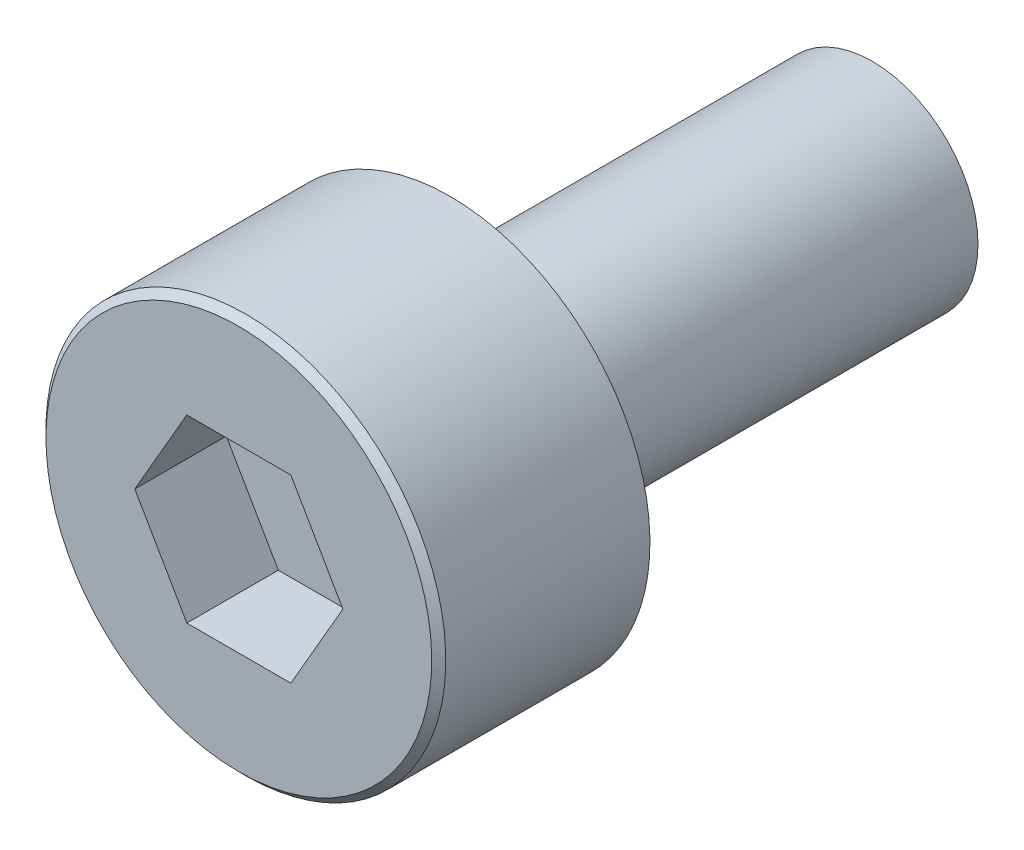
SolidWorks part; units mm, degrees
material "普通碳钢"
ref_plane "前视基准面" through (0, 0, 0) normal (0, 0, 1) x (1, 0, 0)
ref_plane "上视基准面" through (0, 0, 0) normal (0, 1, 0) x (1, 0, 0)
ref_plane "右视基准面" through (0, 0, 0) normal (1, 0, 0) x (0, 0, -1)
sketch "草图1" plane through (0, 0, 0) normal (1, 0, 0) x (0, 0, -1)
  line L0 (0, 0) -> (0, 2.84)
  line L1 (0, 2.84) -> (3, 2.84)
  line L2 (3, 2.84) -> (3, 1.5)
  line L3 (3, 1.5) -> (9, 1.5)
  line L4 (9, 1.5) -> (9, 0)
  line L5 (9, 0) -> (0, 0) construction
  line L6 (0, 0) -> (9, 0)
  dimension "D1" = 5.68
  dimension "D2" = 3
  dimension "D3" = 3
  dimension "D4" = 6
revolve "旋转1" add sketch "草图1" angle 360 about L5
cosmetic thread "装饰螺纹线1" parameters "D2"=1.567
sketch "草图2" plane through (0, 0, 0) normal (0, 0, 1) x (1, 0, 0)
  line L1 (0.739, 1.28) -> (-0.739, 1.28)
  line L2 (-0.739, 1.28) -> (-1.478, 0)
  line L3 (-1.478, 0) -> (-0.739, -1.28)
  line L4 (-0.739, -1.28) -> (0.739, -1.28)
  line L5 (0.739, -1.28) -> (1.478, 0)
  line L6 (1.478, 0) -> (0.739, 1.28)
  circle A0 centre (0, 0) radius 1.28 construction
  dimension "D1" = 2.56
extrude "切除-拉伸1" cut sketch "草图2" against normal blind 1.3
chamfer "装饰倒角" distance 0.1 angle 45 1 edges at (0, 2.84, 0)
